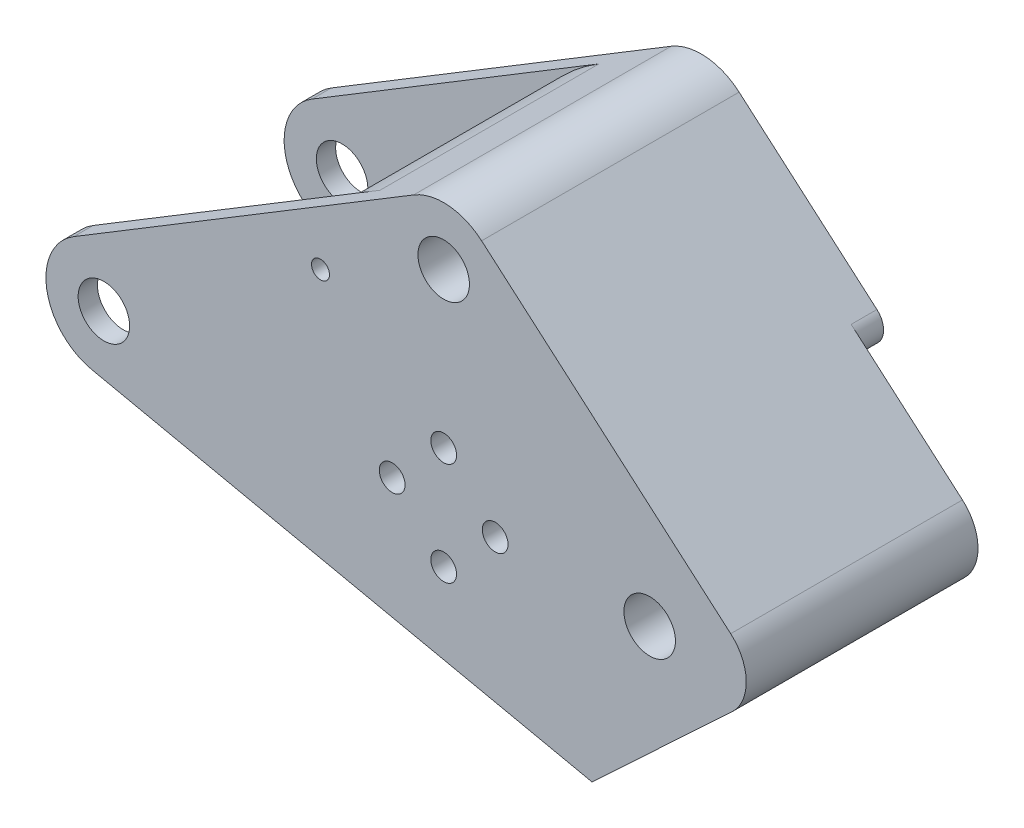
SolidWorks part; units mm, degrees
ref_plane "Front Plane" through (0, 0, 0) normal (0, 0, 1) x (1, 0, 0)
ref_plane "Top Plane" through (0, 0, 0) normal (0, 1, 0) x (1, 0, 0)
ref_plane "Right Plane" through (0, 0, 0) normal (1, 0, 0) x (0, 0, -1)
sketch "Sketch1" plane through (0, 0, 0) normal (0, 0, 1) x (1, 0, 0)
  line L0 (0, 18.4752) -> (52.7846, -12) construction
  line L1 (0, 0) -> (44.7846, 0) construction
  line L2 (-4.6657, 7.6962) -> (48.1189, 39.6962)
  line L3 (58.677, 38.8029) -> (97.3676, 5.2912)
  line L4 (97.5633, -5.1151) -> (75.825, -25.4239)
  line L5 (-1.8827, -8.8009) -> (75.825, -25.4239)
  circle A0 centre (0, 0) radius 4
  circle A1 centre (84.7846, 0) radius 4
  circle A3 centre (60.7846, 0) radius 2
  circle A5 centre (52.7846, -8) radius 2
  circle A6 centre (44.7846, 0) radius 2
  circle A7 centre (52.7846, 8) radius 2
  circle A8 centre (52.7846, 32) radius 4
  circle A9 centre (92.7846, 0) radius 2 construction
  circle A10 centre (84.7846, -8) radius 2 construction
  circle A11 centre (76.7846, 0) radius 2 construction
  circle A12 centre (84.7846, 8) radius 2 construction
  arc A13 (-4.6657, 7.6962) -> (-1.8827, -8.8009) centre (0, 0) ccw
  arc A14 (48.1189, 39.6962) -> (58.677, 38.8029) centre (52.7846, 32) cw
  arc A15 (97.3676, 5.2912) -> (97.5633, -5.1151) centre (92.7846, 0) cw
  point P10 (52.7846, 0)
  point P15 (52.7846, 0)
  point P31 (84.7846, 0)
  dimension "D1" = 8
  dimension "D3" = 4
  dimension "D12" = 5
  dimension "D13" = 5
  dimension "D2" = 8
  dimension "D5" = 32
  dimension "D6" = 32
  dimension "D7" = 16
  dimension "D8" = 30
  dimension "D9" = 2
  dimension "D10" = 8
  dimension "D4" = 4
  dimension "D11" = 4
extrude "Boss-Extrude1" add sketch "Sketch1" along normal mid plane 40
sketch "Sketch2" plane through (0, 0, 0) normal (0, 0, 1) x (1, 0, 0)
  line L0 (-4.6657, 7.6962) -> (39.8919, 34.7087)
  line L1 (48.1189, 39.6962) -> (-4.6657, 7.6962) construction
  line L2 (-1.8827, -8.8009) -> (49.0707, -19.7007)
  line L3 (-1.8827, -8.8009) -> (75.825, -25.4239) construction
  line L4 (22.6274, 0) -> (40.4933, -17.8658) construction
  line L5 (0, 0) -> (22.6274, 0) construction
  arc A0 (-4.6657, 7.6962) -> (-1.8827, -8.8009) centre (0, 0) ccw construction
  arc A1 (-4.6657, 7.6962) -> (-1.8827, -8.8009) centre (0, 0) ccw
  arc A2 (39.8919, 34.7087) -> (49.0707, -19.7007) centre (55.28, 9.3257) ccw
  point P10 (0, 0)
  point P14 (0, 0)
  point P15 (0, 0)
  dimension "D2" = 16
  dimension "D3" = 45
extrude "Cut-Extrude1" cut sketch "Sketch2" against normal offset from surface 3 and the other way offset from surface (17 mm away) 3 up to face at (54.7846, 8, -20) other way up to face at (52.5523, 7.5663, 20)
sketch "Sketch3" plane through (0, 0, -20) normal (0, 0, -1) x (-1, 0, 0)
  circle A30 centre (-52.7846, 8) radius 4
  circle A31 centre (-60.7846, 0) radius 4
  circle A32 centre (-52.7846, -8) radius 4
  circle A33 centre (-44.7846, 0) radius 4
  circle A34 centre (-52.7846, 8) radius 2 construction
  dimension "D1" = 2
extrude "Cut-Extrude2" cut sketch "Sketch3" against normal offset from surface (37 mm away) 3 up to face at (52.5523, 7.5663, 20)
sketch "Sketch4" plane through (0, 0, 20) normal (0, 0, 1) x (1, 0, 0)
  circle A0 centre (33.6505, 22.4275) radius 1.395
  arc A2 (39.8919, 34.7087) -> (49.0707, -19.7007) centre (55.28, 9.3257) ccw construction
  circle A3 centre (52.7846, 32) radius 4 construction
  point P7 (33.6715, 19.8509)
  dimension "D1" = 3
  dimension "D2" = 20
  dimension "D3" = 2.79
extrude "Cut-Extrude3" cut sketch "Sketch4" against normal through all
sketch "Sketch5" plane through (0, 0, -20) normal (0, 0, -1) x (-1, 0, 0)
  line L0 (-75.825, -25.4239) -> (-97.5633, -5.1151) construction
  line L1 (-97.3676, 5.2912) -> (-58.677, 38.8029) construction
  line L2 (-97.3676, 5.2912) -> (-84.7846, 16.1899)
  line L3 (-97.5633, -5.1151) -> (-85.7391, -16.1617)
  arc A0 (-85.7391, -16.1617) -> (-84.7846, 16.1899) centre (-84.7846, 0) ccw
  arc A1 (-97.3676, 5.2912) -> (-97.5633, -5.1151) centre (-92.7846, 0) ccw construction
  arc A2 (-97.3676, 5.2912) -> (-97.5633, -5.1151) centre (-92.7846, 0) ccw
  point P8 (-73.6401, 16.1623)
  point P11 (-85.9353, 15.1932)
extrude "Cut-Extrude4" cut sketch "Sketch5" against normal blind 4
fillet "Fillet1" radius 3 2 edges at (85.7391, -16.1617, -18) (84.7846, 16.1899, -18)
